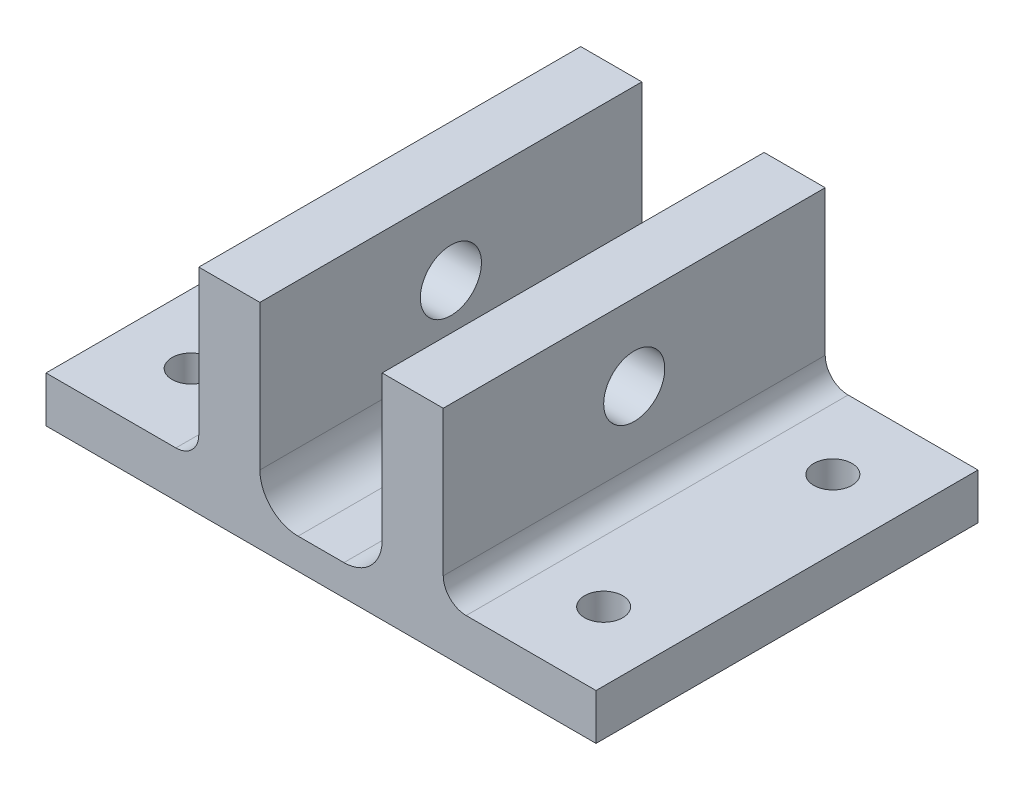
SolidWorks part; units mm, degrees
ref_plane "Front Plane" through (0, 0, 0) normal (0, 0, 1) x (1, 0, 0)
ref_plane "Top Plane" through (0, 0, 0) normal (0, 1, 0) x (1, 0, 0)
ref_plane "Right Plane" through (0, 0, 0) normal (1, 0, 0) x (0, 0, -1)
sketch "Sketch1" plane through (0, 0, 0) normal (0, 0, 1) x (1, 0, 0)
  line L0 (0, 0) -> (0, 28) construction
  line L1 (0, 28) -> (-8, 28)
  line L2 (-8, 28) -> (-8, 4)
  line L3 (-8, 4) -> (-24, 4)
  line L5 (-32, 0) -> (0, 0)
  line L6 (-32, 0) -> (-32, 28) construction
  line L7 (-32, 28) -> (-24, 28)
  line L8 (-24, 28) -> (-24, 4)
  line L9 (-32, 0) -> (-52, 0)
  line L10 (-52, 0) -> (-52, 6)
  line L11 (-52, 6) -> (-32, 6)
  line L12 (-32, 6) -> (-32, 28)
  line L13 (0, 0) -> (20, 0)
  line L14 (20, 0) -> (20, 6)
  line L15 (20, 6) -> (0, 6)
  line L16 (0, 6) -> (0, 28)
  dimension "D1" = 8
  dimension "D2" = 4
  dimension "D3" = 28
  dimension "D4" = 16
  dimension "D5" = 8
  dimension "D6" = 6
  dimension "D7" = 20
  dimension "D8" = 20
extrude "Boss-Extrude1" add sketch "Sketch1" along normal mid plane 50 contours L5 L13 L14 L15 L16 L1 L2 L3 L8 L7 L12 L11 L10 L9
sketch "Sketch2" plane through (-8, 0, 0) normal (-1, 0, 0) x (0, 0, 1)
  line L0 (25, 28) -> (-25, 28) construction
  circle A0 centre (0, 18) radius 4
  dimension "D1" = 8
  dimension "D2" = 10
extrude "Cut-Extrude1" cut sketch "Sketch2" against normal through all both and the other way through all
sketch "Sketch3" plane through (0, 4, 0) normal (0, 1, 0) x (1, 0, 0)
  line L0 (0, 0) -> (-52, 0) construction
  line L2 (-16, 25) -> (-16, -25) construction
  line L3 (-8, 25) -> (-24, 25) construction
  line L4 (-8, -25) -> (-24, -25) construction
  line L5 (-52, -25) -> (-52, 25) construction
  circle A0 centre (-43, 15) radius 2.5
  circle A1 centre (11, 15) radius 2.5
  circle A2 centre (11, -15) radius 2.5
  circle A3 centre (-43, -15) radius 2.5
  point P11 (-58, 0)
  point P17 (0, 0)
  point P18 (-17, -15)
  dimension "D1" = 5
  dimension "D2" = 15
  dimension "D3" = 27
fillet "Fillet1" radius 3 2 edges at (0, 6, 0) (-32, 6, 0)
fillet "Fillet2" radius 5 2 edges at (-8, 4, 0) (-24, 4, 0)
extrude "Cut-Extrude2" cut sketch "Sketch3" against normal through all both and the other way through all
